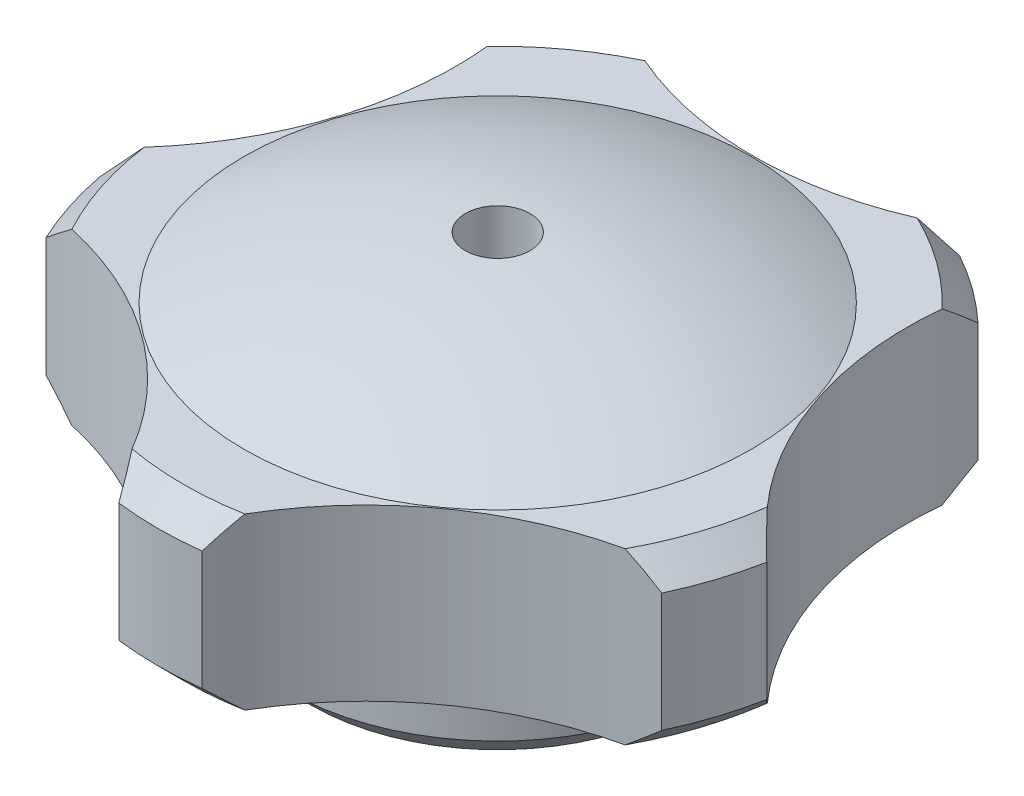
SolidWorks part; units mm, degrees
ref_plane "Face" through (0, 0, 0) normal (0, 0, 1) x (1, 0, 0)
ref_plane "Dessus" through (0, 0, 0) normal (0, 1, 0) x (1, 0, 0)
ref_plane "Droite" through (0, 0, 0) normal (1, 0, 0) x (0, 0, -1)
sketch "Esquisse1" plane through (0, 0, 0) normal (0, 0, 1) x (1, 0, 0)
  line L0 (-0.38, 0) -> (-2.5, 0)
  line L1 (-2.5, 0) -> (-2.5, 1)
  line L2 (-2.5, 1) -> (-4, 1)
  line L3 (-4, 1) -> (-4, 3)
  line L4 (0, 0) -> (0, 14.1388) construction
  line L5 (-4, 3) -> (-2.9859, 3)
  line L6 (-0.38, 3) -> (-0.38, 0)
  line L7 (-0.38, 0) -> (0, 0) construction
  line L8 (-0.38, 3) -> (-0.38, 3.7217)
  arc A0 (-2.9859, 3) -> (-0.38, 3.7217) centre (0.0788, -3.0004) cw
  dimension "D1" = 0.76
  dimension "D2" = 5
  dimension "D3" = 8
  dimension "D4" = 1
  dimension "D5" = 2
revolve "Révolution1" add sketch "Esquisse1" angle 360 about L4
chamfer "Chanfrein1" distance 0.3 angle 45 3 edges at (0, 0, -2.5) (0, 1, -4) (0, 3, -4)
sketch "Esquisse2" plane through (0, 3, 0) normal (0, 1, 0) x (1, 0, 0)
  line L0 (0, 0) -> (0, 7) construction
  circle A0 centre (0, 7) radius 4
  dimension "D2" = 8
  dimension "D1" = 3
extrude "Enlèv. mat.-Extru.1" cut sketch "Esquisse2" against normal up to next (2 mm away)
pattern_circular "Répétition circulaire1" count 5 over 360 about axis through (0, 0, 0) along (0, 1, 0) of "Enlèv. mat.-Extru.1"
